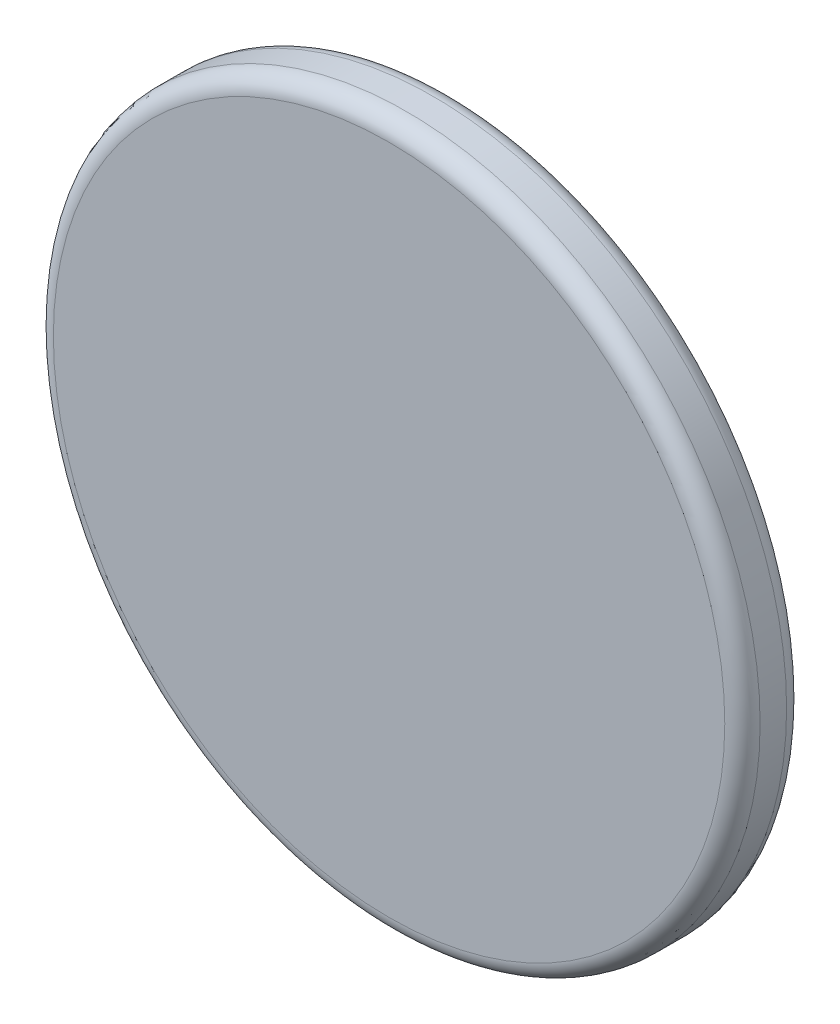
SolidWorks part; units mm, degrees
ref_plane "Front Plane" through (0, 0, 0) normal (0, 0, 1) x (1, 0, 0)
ref_plane "Top Plane" through (0, 0, 0) normal (0, 1, 0) x (1, 0, 0)
ref_plane "Right Plane" through (0, 0, 0) normal (1, 0, 0) x (0, 0, -1)
sketch "Sketch1" plane through (0, 0, 0) normal (0, 0, 1) x (1, 0, 0)
  circle A0 centre (0, 0) radius 40
  dimension "D1" = 80
extrude "Boss-Extrude1" add sketch "Sketch1" along normal blind 7
fillet "Fillet1" radius 2 1 edges at (40, 0, 0)
fillet "Fillet2" radius 2 1 edges at (40, 0, 7)
